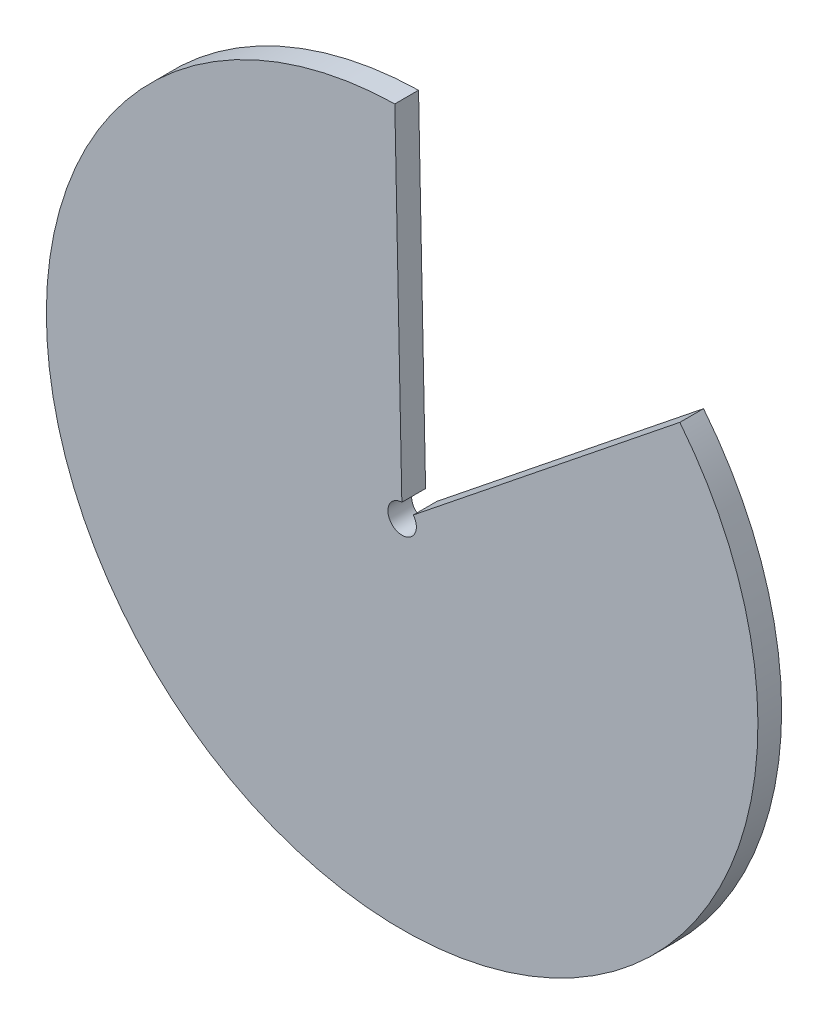
SolidWorks part; units mm, degrees
ref_plane "Front Plane" through (0, 0, 0) normal (0, 0, 1) x (1, 0, 0)
ref_plane "Top Plane" through (0, 0, 0) normal (0, 1, 0) x (1, 0, 0)
ref_plane "Right Plane" through (0, 0, 0) normal (1, 0, 0) x (0, 0, -1)
sketch "Sketch1" plane through (0, 0, 0) normal (0, 0, 1) x (1, 0, 0)
  circle A0 centre (0, 0) radius 38.1
  dimension "D1" = 76.2
extrude "Boss-Extrude1" add sketch "Sketch1" along normal blind 2.54
sketch "Sketch2" plane through (0, 0, 2.54) normal (0, 0, 1) x (1, 0, 0)
  line L0 (0, 0) -> (-0.7838, 38.0919)
  line L1 (0, 0) -> (29.7357, 23.8201)
  circle A0 centre (0, 0) radius 38.1 construction
  arc A1 (29.7357, 23.8201) -> (-0.7838, 38.0919) centre (0, 0) ccw
extrude "Cut-Extrude1" cut sketch "Sketch2" against normal blind 2.54
sketch "Sketch3" plane through (0, 0, 2.54) normal (0, 0, 1) x (1, 0, 0)
  circle A0 centre (0, 0) radius 1.524
  dimension "D1" = 3.048
extrude "Cut-Extrude2" cut sketch "Sketch3" against normal blind 2.54
